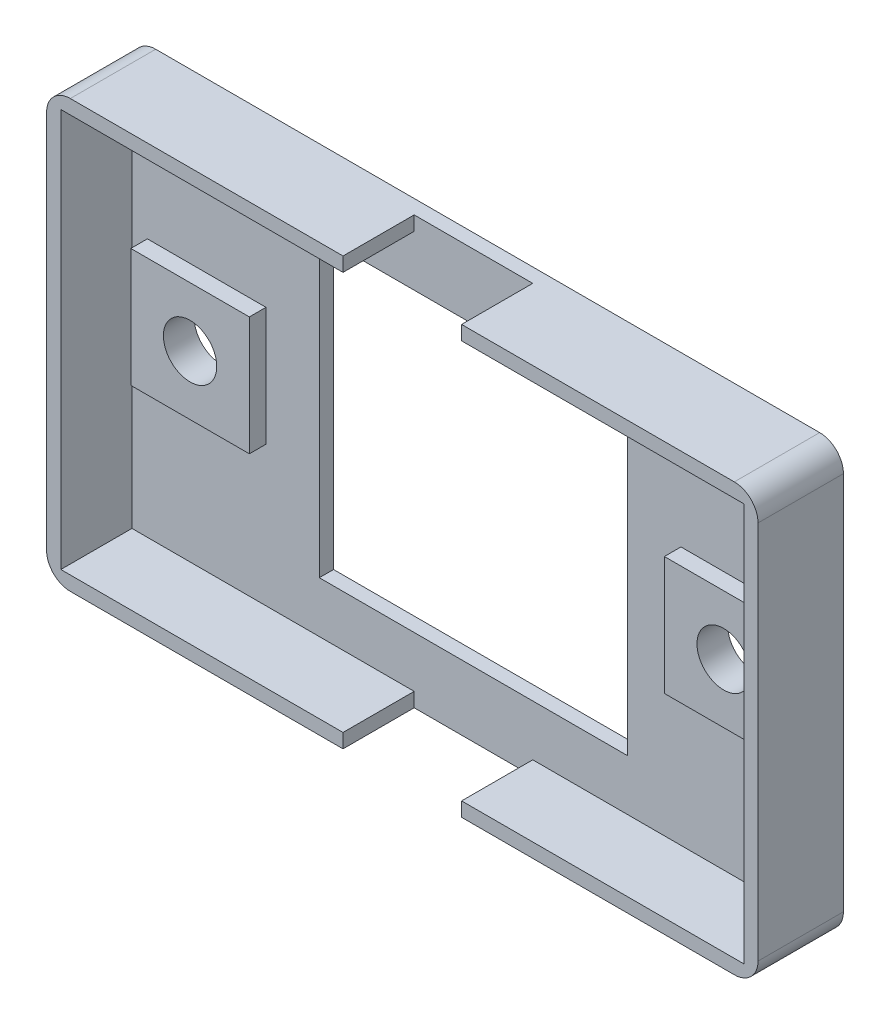
SolidWorks part; units mm, degrees
ref_plane "Přední rovina" through (0, 0, 0) normal (0, 0, 1) x (1, 0, 0)
ref_plane "Horní rovina" through (0, 0, 0) normal (0, 1, 0) x (1, 0, 0)
ref_plane "Pravá rovina" through (0, 0, 0) normal (1, 0, 0) x (0, 0, -1)
sketch "Skica1" plane through (0, 0, 0) normal (0, 0, 1) x (1, 0, 0)
  line L1 (-30, 18) -> (30, 18)
  line L2 (-30, 18) -> (-30, -18)
  line L3 (-30, -18) -> (30, -18)
  line L4 (30, 18) -> (30, -18)
  line L5 (-30, 18) -> (30, -18) construction
  line L6 (-30, -18) -> (30, 18) construction
  line L7 (-13, 12.5) -> (13, 12.5)
  line L8 (-13, 12.5) -> (-13, -12.5)
  line L9 (-13, -12.5) -> (13, -12.5)
  line L10 (13, 12.5) -> (13, -12.5)
  line L11 (-13, 12.5) -> (13, -12.5) construction
  line L12 (-13, -12.5) -> (13, 12.5) construction
  point P0 (0, 0)
  point P6 (0, 0)
  dimension "D1" = 36
  dimension "D2" = 60
  dimension "D3" = 26
  dimension "D4" = 25
extrude "Přidat vysunutím1" add sketch "Skica1" along normal blind 1.2
sketch "Skica2" plane through (0, 0, 1.2) normal (0, 0, 1) x (1, 0, 0)
  line L0 (0, 0) -> (22.5, 0)
  line L1 (0, 0) -> (0, -8.029)
  line L2 (17.5, 5) -> (27.5, 5)
  line L3 (17.5, 5) -> (17.5, -5)
  line L4 (17.5, -5) -> (27.5, -5)
  line L5 (27.5, 5) -> (27.5, -5)
  line L6 (17.5, 5) -> (27.5, -5) construction
  line L7 (17.5, -5) -> (27.5, 5) construction
  line L8 (-17.5, -5) -> (-27.5, -5)
  line L9 (-27.5, 5) -> (-27.5, -5)
  line L10 (-17.5, 5) -> (-27.5, 5)
  line L11 (-17.5, 5) -> (-17.5, -5)
  dimension "D1" = 22.5
  dimension "D2" = 10
  dimension "D3" = 10
extrude "Přidat vysunutím2" add sketch "Skica2" along normal blind 1.4
sketch "Skica3" plane through (0, 0, 1.2) normal (0, 0, 1) x (1, 0, 0)
  line L0 (-28.8, 16.8) -> (-28.8, -16.8)
  line L1 (-30, 18) -> (30, 18)
  line L2 (-30, 18) -> (-30, -18)
  line L3 (-30, -18) -> (30, -18)
  line L4 (30, 18) -> (30, -18)
  line L5 (-30, 18) -> (30, -18) construction
  line L6 (-30, -18) -> (30, 18) construction
  line L7 (-28.8, -16.8) -> (28.8, -16.8)
  line L8 (28.8, 16.8) -> (28.8, -16.8)
  line L9 (-28.8, 16.8) -> (28.8, 16.8)
  line L10 (0, 16.8) -> (0, 18)
  line L11 (0, 0) -> (6.7191, 0)
  line L12 (-5, 18) -> (5, 18)
  line L13 (-5, 18) -> (-5, 16.8)
  line L14 (-5, 16.8) -> (5, 16.8)
  line L15 (5, 18) -> (5, 16.8)
  line L16 (-5, 18) -> (5, 16.8) construction
  line L17 (-5, 16.8) -> (5, 18) construction
  line L18 (-5, -18) -> (-5, -16.8)
  line L19 (5, -18) -> (5, -16.8)
  point P0 (0, 0)
  point P13 (0, 17.4)
  line M16 (30, -18) -> (30, 18)
  line M17 (30, 18) -> (-30, 18)
  line M18 (-30, 18) -> (-30, -18)
  line M19 (-30, -18) -> (30, -18)
  dimension "D2" = 10
  dimension "D1" = 1.2
extrude "Přidat vysunutím3" add sketch "Skica3" along normal blind 6 contours L18 L7 L0 L9 L13 M19 M17 M18 | L19 L15 L9 L8 L7 M19 M16 M17
sketch "Skica4" plane through (0, 0, 2.6) normal (0, 0, 1) x (1, 0, 0)
  point P0 (22.5, 0)
  point P1 (-22.5, 0)
hole_wizard "M4 díra s vůlí1" positions "Skica5" profile "Skica6" hole size "M4" standard "ISO" end condition through all
sketch "Skica5" plane through (0, 0, 2.6) normal (0, 0, 1) x (1, 0, 0)
  point P0 (-22.5, 0)
  point P3 (22.5, 0)
sketch "Skica6" plane through (-22.5, 0, 2.6) normal (1, 0, 0) x (0, -1, 0)
  line L0 (0, 0) -> (0, 2.6)
  line L1 (0, 2.6) -> (2.25, 2.6)
  line L2 (2.25, 2.6) -> (2.25, 0)
  line L5 (2.25, 0) -> (0, 0)
  line L11 (0, -6.35) -> (0, 107.95) construction
  dimension "Průměr díry skrz" = 4.5
  dimension "Hloubka díry skrz" = 2.6
fillet "Zaoblit1" radius 2 4 edges at (-30, 18, 3.6) (-30, -18, 3.6) (30, 18, 3.6) (30, -18, 3.6)
